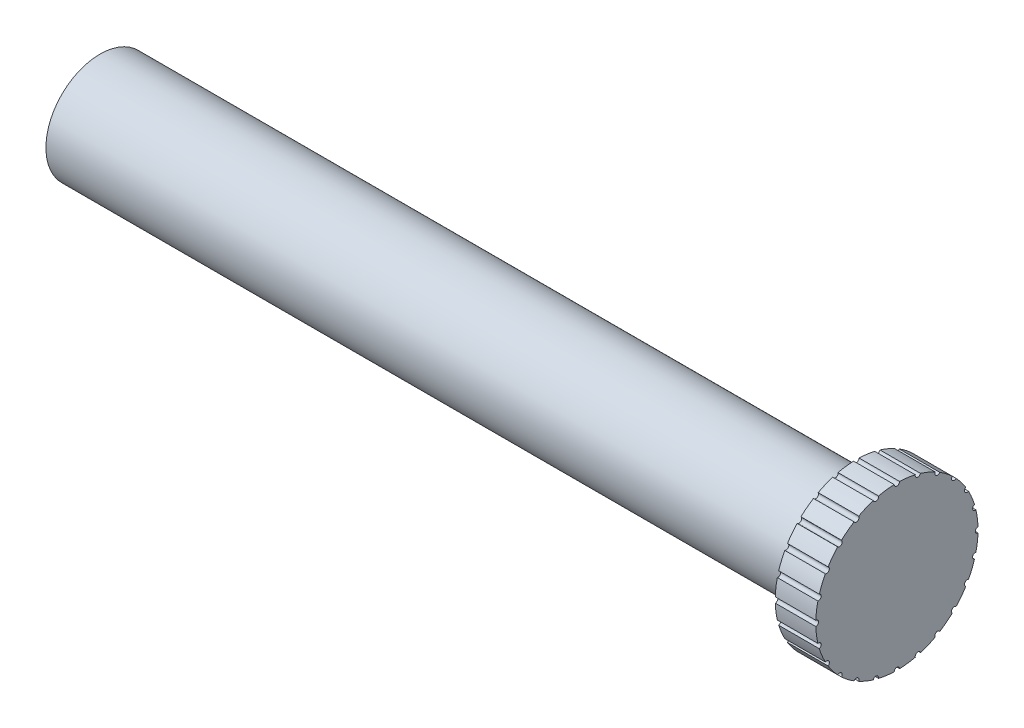
SolidWorks part; units mm, degrees
ref_plane "Ön Düzlem" through (0, 0, 0) normal (0, 0, 1) x (1, 0, 0)
ref_plane "Üst Düzlem" through (0, 0, 0) normal (0, 1, 0) x (1, 0, 0)
ref_plane "Sağ Düzlem" through (0, 0, 0) normal (1, 0, 0) x (0, 0, -1)
sketch "Sketch1" plane through (0, 0, 0) normal (1, 0, 0) x (0, 0, -1)
  circle A0 centre (0, 0) radius 4
extrude "Boss-Extrude1" add sketch "Sketch1" along normal blind 55.94
sketch "Sketch2" plane through (55.94, 0, 0) normal (1, 0, 0) x (0, 0, -1)
  circle A0 centre (0, 0) radius 6
extrude "Boss-Extrude2" add sketch "Sketch2" along normal blind 3
sketch "Sketch3" plane through (58.94, 0, 0) normal (1, 0, 0) x (0, 0, -1)
  circle A0 centre (-6, 0) radius 0.2
  circle A1 centre (0, 0) radius 6 construction
extrude "Cut-Extrude1" cut sketch "Sketch3" against normal up to surface (3 mm away) up to face at (55.94, 0, -4)
pattern_circular "CirPattern1" count 25 every 15 about axis through (0, 0, 0) along (1, 0, 0) of "Cut-Extrude1"
